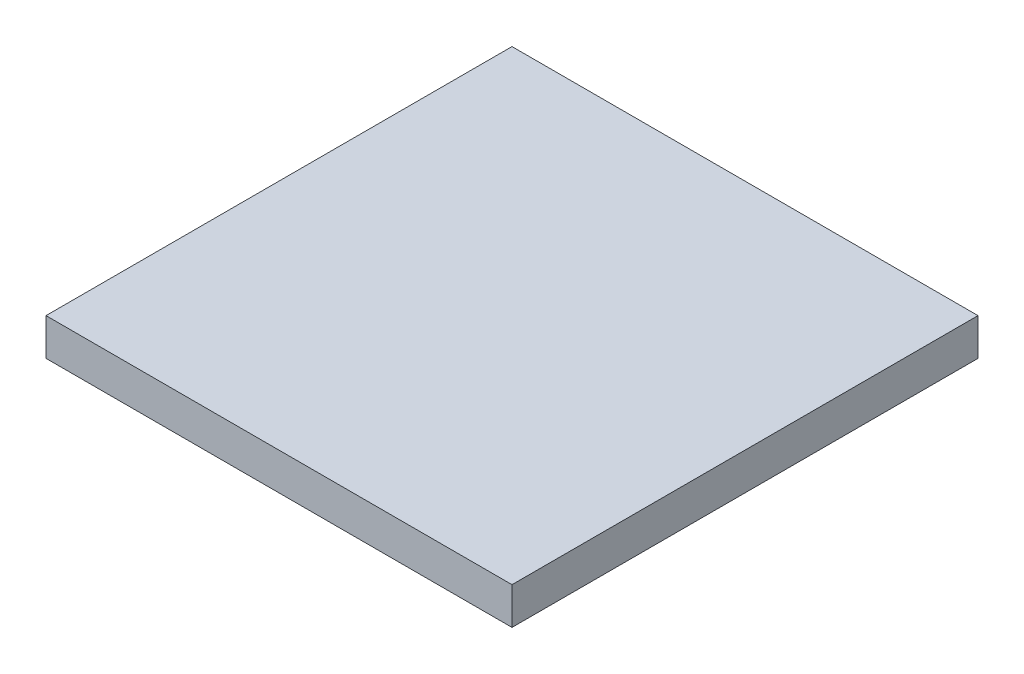
SolidWorks part; units mm, degrees
ref_plane "Front Plane" through (0, 0, 0) normal (0, 0, 1) x (1, 0, 0)
ref_plane "Top Plane" through (0, 0, 0) normal (0, 1, 0) x (1, 0, 0)
ref_plane "Right Plane" through (0, 0, 0) normal (1, 0, 0) x (0, 0, -1)
sketch "Sketch3" plane through (0, 0, 0) normal (0, 1, 0) x (1, 0, 0)
  line L1 (0, 0) -> (20, 0)
  line L2 (0, 0) -> (0, 20)
  line L3 (0, 20) -> (20, 20)
  line L4 (20, 0) -> (20, 20)
  dimension "D1" = 20
  dimension "D2" = 20
extrude "Boss-Extrude1" add sketch "Sketch3" along normal blind 1.59
sketch "Sketch7" plane through (0, 1.59, 0) normal (0, 1, 0) x (1, 0, 0)
  line L0 (0, 10) -> (20, 10)
  line L1 (0, 20) -> (0, 0) construction
  line L2 (11.27, 10) -> (11.27, 0)
  line L3 (10, 10) -> (10, 0) construction
  line L4 (0, 0) -> (20, 0) construction
  line L5 (20, 0) -> (20, 20) construction
  line L6 (0, 20) -> (0, 0) construction
  line L7 (0, 0) -> (20, 0) construction
  line L8 (20, 20) -> (0, 20) construction
  line L9 (18.5, 1.5) -> (1.5, 1.5) construction
  circle A0 centre (1.5, 1.5) radius 0.35
  circle A1 centre (10, 18.5) radius 0.35
  circle A2 centre (18.5, 1.5) radius 0.35
  point P2 (10, 1.5)
  point P14 (0, 10)
  point P23 (10, 0)
  dimension "D5" = 0.7
  dimension "D1" = 1.5
  dimension "D2" = 1.5
  dimension "D3" = 1.5
  dimension "D4" = 1.27
